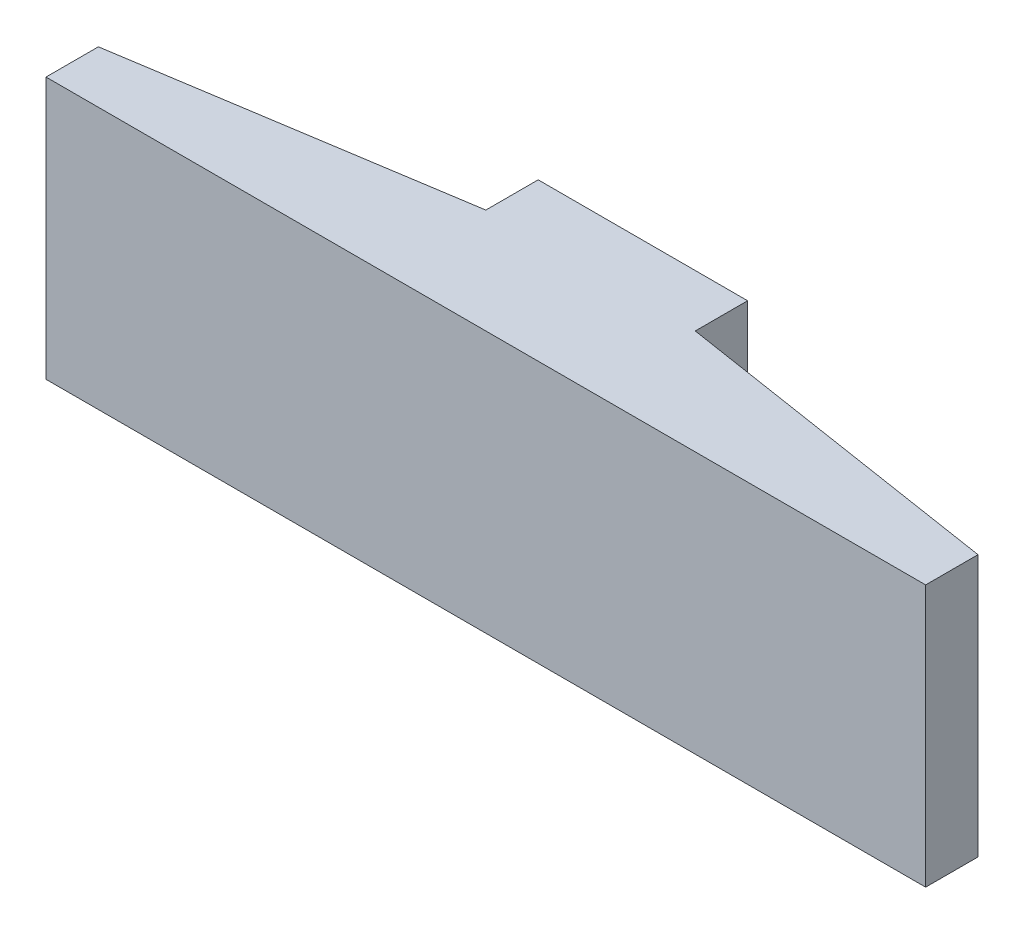
SolidWorks part; units mm, degrees
ref_plane "Přední rovina" through (0, 0, 0) normal (0, 0, 1) x (1, 0, 0)
ref_plane "Horní rovina" through (0, 0, 0) normal (0, 1, 0) x (1, 0, 0)
ref_plane "Pravá rovina" through (0, 0, 0) normal (1, 0, 0) x (0, 0, -1)
sketch "Skica1" plane through (0, 0, 0) normal (0, 1, 0) x (1, 0, 0)
  line L1 (4.2, -0.75) -> (-4.2, -0.75)
  line L2 (4.2, -0.75) -> (4.2, -0.25)
  line L3 (1, 0.75) -> (-1, 0.75)
  line L4 (-4.2, -0.75) -> (-4.2, -0.25)
  line L6 (1, 0.25) -> (1, 0.75)
  line L8 (-1, 0.25) -> (-1, 0.75)
  line L10 (-4.2, -0.25) -> (-1, 0.25)
  line L11 (1, 0.25) -> (4.2, -0.25)
  point P0 (0, 0)
  point P6 (0, 0)
  point P8 (0, 0)
  dimension "D1" = 8.4
extrude "Přidat vysunutím1" add sketch "Skica1" along normal blind 2.5 contours L3 L8 L10 L4 L1 L2 L11 L6
